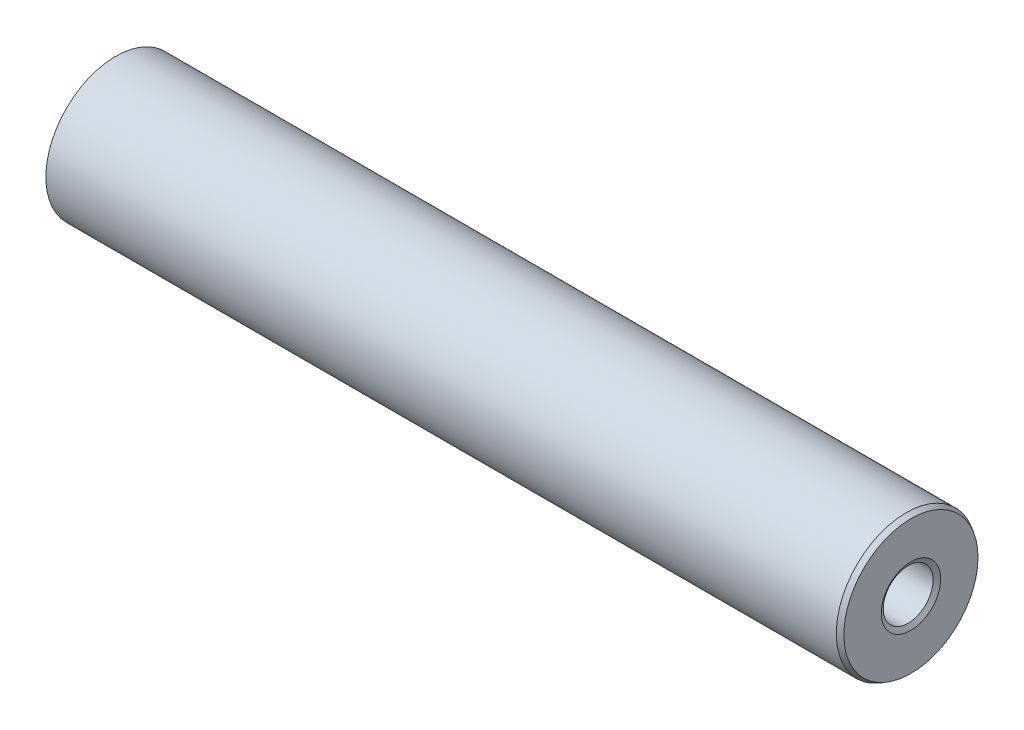
SolidWorks part; units mm, degrees
material "6061-T6 (SS)"
ref_plane "Front Plane" through (0, 0, 0) normal (0, 0, 1) x (1, 0, 0)
ref_plane "Top Plane" through (0, 0, 0) normal (0, 1, 0) x (1, 0, 0)
ref_plane "Right Plane" through (0, 0, 0) normal (1, 0, 0) x (0, 0, -1)
sketch "Sketch1" plane through (0, 0, 0) normal (1, 0, 0) x (0, 0, -1)
  circle A0 centre (0, 0) radius 3.9688
  circle A1 centre (0, 0) radius 11.1125
  dimension "D1" = 22.225
  dimension "D2" = 7.9375
extrude "Boss-Extrude1" add sketch "Sketch1" along normal blind 127
chamfer "Chamfer1" distance 0.762 angle 30 4 edges at (127, 0, -11.1125) (127, 0, -3.9688) (0, 0, -3.9688) (0, 0, -11.1125)
